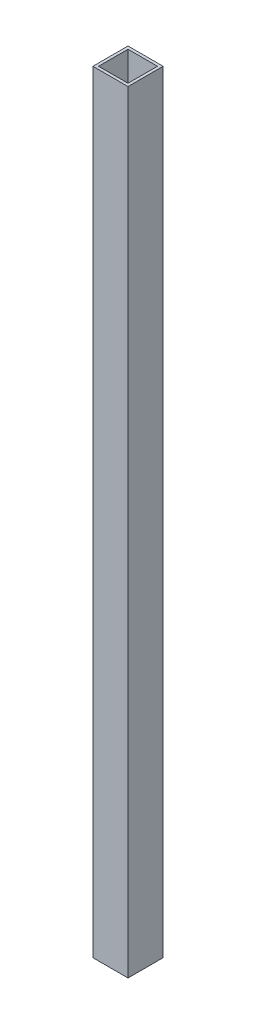
SolidWorks part; units mm, degrees
ref_plane "Спереди" through (0, 0, 0) normal (0, 0, 1) x (1, 0, 0)
ref_plane "Сверху" through (0, 0, 0) normal (0, 1, 0) x (1, 0, 0)
ref_plane "Справа" through (0, 0, 0) normal (1, 0, 0) x (0, 0, -1)
sketch "Эскиз1" plane through (0, 0, 0) normal (0, 1, 0) x (1, 0, 0)
  line L1 (-12.5, -12.5) -> (12.5, -12.5)
  line L2 (-12.5, -12.5) -> (-12.5, 12.5)
  line L3 (-12.5, 12.5) -> (12.5, 12.5)
  line L4 (12.5, -12.5) -> (12.5, 12.5)
  line L5 (-12.5, -12.5) -> (12.5, 12.5) construction
  line L6 (-12.5, 12.5) -> (12.5, -12.5) construction
  point P0 (0, 0)
extrude "Вытянуть-Тонкостенный1" add sketch "Эскиз1" along normal blind 550 thin thin type one direction reverse wall 2
